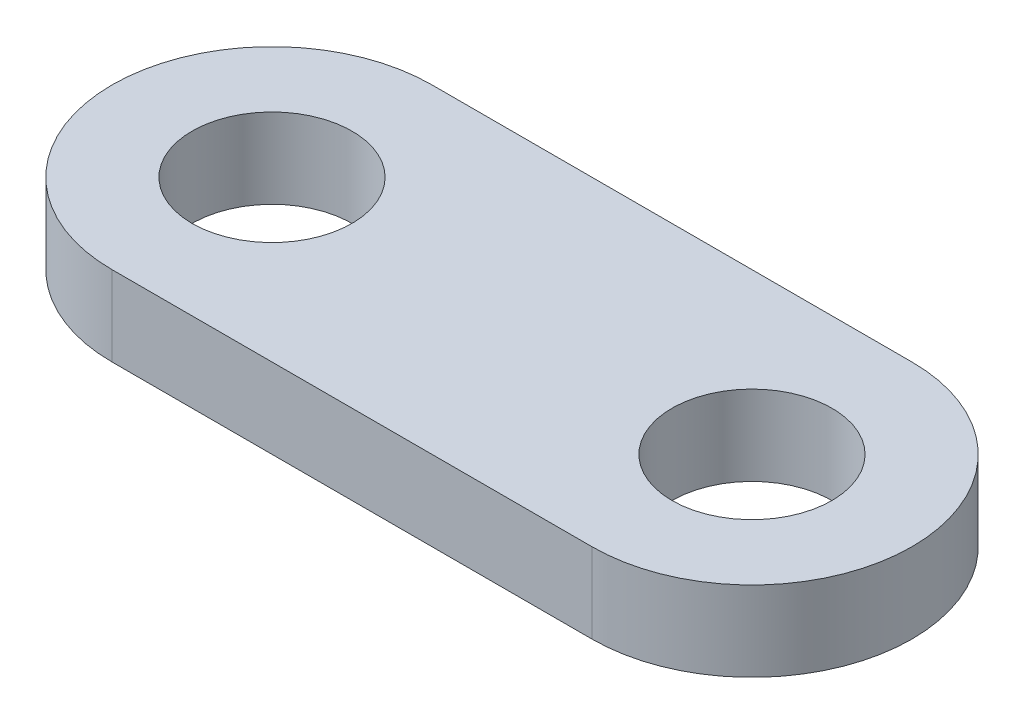
SolidWorks part; units mm, degrees
ref_plane "Front Plane" through (0, 0, 0) normal (0, 0, 1) x (1, 0, 0)
ref_plane "Top Plane" through (0, 0, 0) normal (0, 1, 0) x (1, 0, 0)
ref_plane "Right Plane" through (0, 0, 0) normal (1, 0, 0) x (0, 0, -1)
sketch "Sketch1" plane through (0, 0, 0) normal (0, 1, 0) x (1, 0, 0)
  line L0 (0, 0) -> (30, 0) construction
  line L1 (0, 10) -> (30, 10)
  line L2 (0, -10) -> (30, -10)
  arc A0 (0, 10) -> (0, -10) centre (0, 0) ccw
  arc A1 (30, -10) -> (30, 10) centre (30, 0) ccw
  circle A2 centre (0, 0) radius 5
  circle A3 centre (30, 0) radius 5
  point P3 (15, 0)
  dimension "D2" = 10
  dimension "D3" = 10
  dimension "D4" = 10
  dimension "D1" = 30
extrude "Boss-Extrude1" add sketch "Sketch1" along normal blind 5
